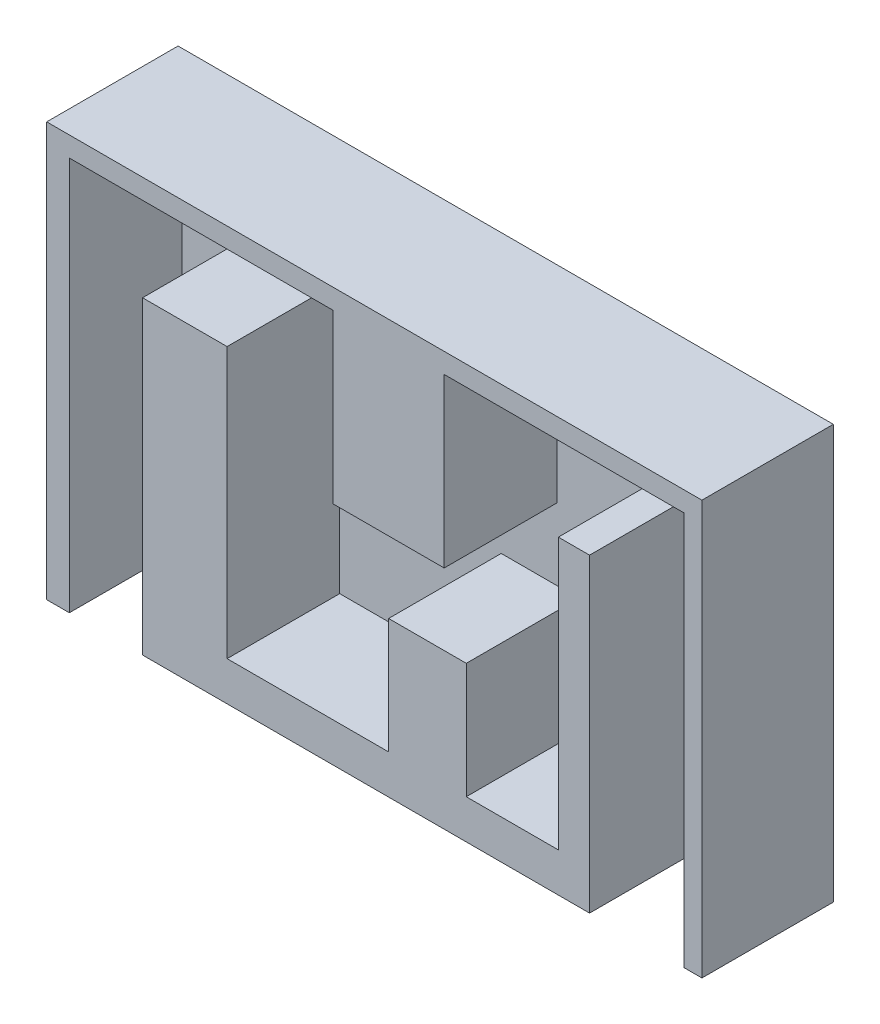
SolidWorks part; units mm, degrees
ref_plane "Front Plane" through (0, 0, 0) normal (0, 0, 1) x (1, 0, 0)
ref_plane "Top Plane" through (0, 0, 0) normal (0, 1, 0) x (1, 0, 0)
ref_plane "Right Plane" through (0, 0, 0) normal (1, 0, 0) x (0, 0, -1)
sketch "Sketch1" plane through (0, 0, 0) normal (0, 0, 1) x (1, 0, 0)
  line L1 (-8052.5373, 4999.0584) -> (9403.6342, 4999.0584)
  line L2 (-8052.5373, 4999.0584) -> (-8052.5373, -6025.892)
  line L3 (-8052.5373, -6025.892) -> (9403.6342, -6025.892)
  line L4 (9403.6342, 4999.0584) -> (9403.6342, -6025.892)
extrude "Boss-Extrude1" add sketch "Sketch1" along normal blind 500
sketch "Sketch2" plane through (0, 0, 500) normal (0, 0, 1) x (1, 0, 0)
  line L0 (9403.6342, 4999.0584) -> (-8052.5373, 4999.0584) construction
  line L1 (-8052.5373, -6025.892) -> (-7448.8074, -6025.892)
  line L2 (-8052.5373, -6025.892) -> (-8052.5373, 4999.0584)
  line L3 (-8052.5373, 4999.0584) -> (-7448.8074, 4999.0584)
  line L4 (-7448.8074, -6025.892) -> (-7448.8074, 4466.4628)
  line L5 (-8052.5373, -6025.892) -> (9403.6342, -6025.892) construction
  line L6 (-7448.8074, 4999.0584) -> (9403.6342, 4999.0584)
  line L7 (3125.3062, -4983.0329) -> (5578.0197, -4983.0329)
  line L8 (-7448.8074, 4466.4628) -> (-423.4371, 4466.4628)
  line L9 (9403.6342, 4999.0584) -> (9403.6342, 4466.4628)
  line L10 (2536.6868, 4466.4628) -> (8924.3887, 4466.4628)
  line L11 (9403.6342, 4466.4628) -> (9403.6342, -6025.892)
  line L12 (9403.6342, -6025.892) -> (8924.3887, -6025.892)
  line L13 (8924.3887, 4466.4628) -> (8924.3887, -6025.892)
  line L15 (-5498.8477, -6025.892) -> (-3246.4774, -6025.892)
  line L16 (-5498.8477, -6025.892) -> (-5498.8477, 2217.43)
  line L17 (-5498.8477, 2217.43) -> (-3246.4774, 2217.43)
  line L18 (-3246.4774, -4983.0329) -> (-3246.4774, 2217.43)
  line L20 (-423.4371, 4466.4628) -> (-423.4371, 0)
  line L21 (-423.4371, 0) -> (2536.6868, 0)
  line L22 (2536.6868, 4466.4628) -> (2536.6868, 0)
  line L23 (-3246.4774, -4983.0329) -> (1056.6248, -4983.0329)
  line L25 (-3246.4774, -6025.892) -> (6409.7547, -6025.892)
  line L26 (6409.7547, -4983.0329) -> (6409.7547, -6025.892)
  line L28 (1056.6248, -4983.0329) -> (1056.6248, -1904.231)
  line L29 (1056.6248, -1904.231) -> (3125.3062, -1904.231)
  line L30 (3125.3062, -4983.0329) -> (3125.3062, -1904.231)
  line L32 (6409.7547, -4983.0329) -> (6409.7547, 2233.2314)
  line L33 (6409.7547, 2233.2314) -> (5578.0197, 2233.2314)
  line L34 (5578.0197, -4983.0329) -> (5578.0197, 2233.2314)
extrude "Boss-Extrude2" add sketch "Sketch2" along normal blind 3000
